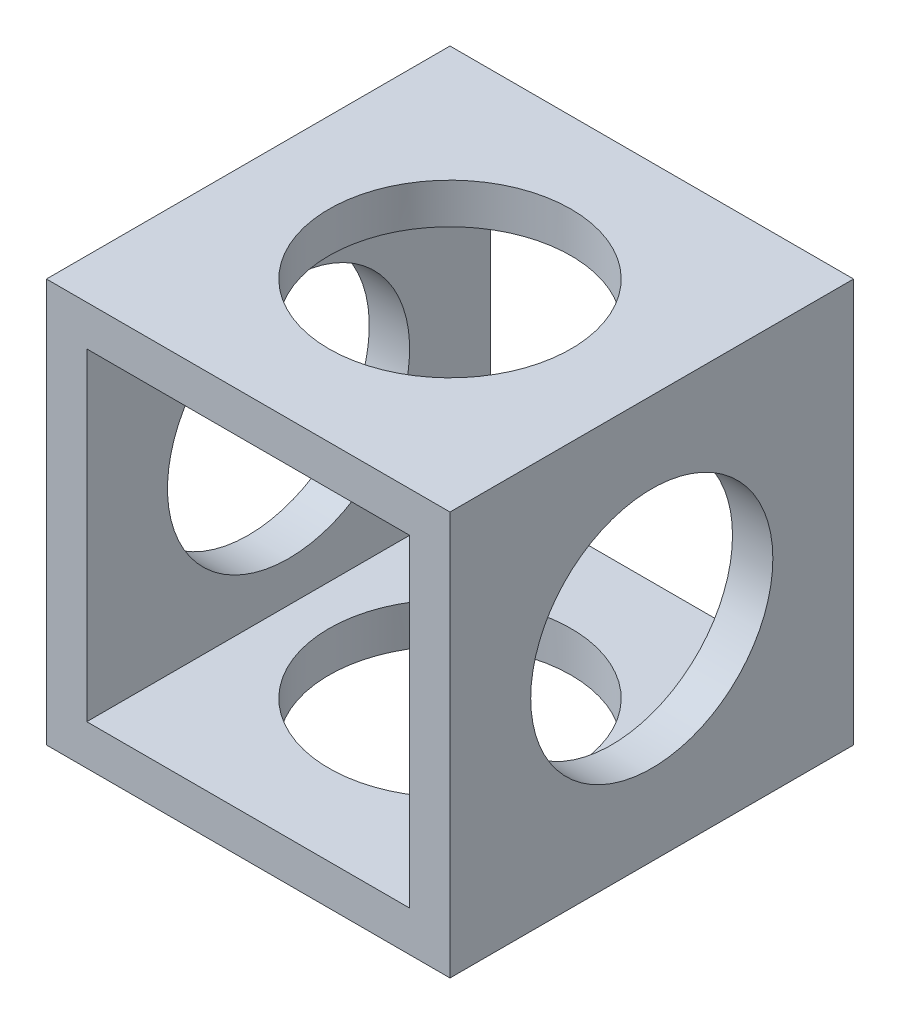
SolidWorks part; units mm, degrees
ref_plane "Alzado" through (0, 0, 0) normal (0, 0, 1) x (1, 0, 0)
ref_plane "Planta" through (0, 0, 0) normal (0, 1, 0) x (1, 0, 0)
ref_plane "Vista lateral" through (0, 0, 0) normal (1, 0, 0) x (0, 0, -1)
sketch "Croquis1" plane through (0, 0, 0) normal (0, 0, 1) x (1, 0, 0)
  line L1 (-25, -25) -> (25, -25)
  line L2 (-25, -25) -> (-25, 25)
  line L3 (-25, 25) -> (25, 25)
  line L4 (25, -25) -> (25, 25)
  line L5 (-25, -25) -> (25, 25) construction
  line L6 (-25, 25) -> (25, -25) construction
  line L7 (-20, -20) -> (20, -20)
  line L8 (-20, -20) -> (-20, 20)
  line L9 (-20, 20) -> (20, 20)
  line L10 (20, -20) -> (20, 20)
  line L11 (-20, -20) -> (20, 20) construction
  line L12 (-20, 20) -> (20, -20) construction
  point P0 (0, 0)
  point P6 (0, 0)
  point P11 (25, 28.1863)
  point P12 (25, 0)
  dimension "D1" = 50
  dimension "D2" = 50
  dimension "D3" = 5
extrude "Saliente-Extruir1" add sketch "Croquis1" against normal blind 50
sketch "Croquis2" plane through (0, 25, 0) normal (0, 1, 0) x (1, 0, 0)
  line L0 (25, 50) -> (25, 0) construction
  line L1 (25, 50) -> (25, 0)
  circle A0 centre (0, 25) radius 15
  point P4 (0, 0)
  point P5 (25, 25)
  point P6 (-4.8349, 25)
  dimension "D1" = 30
extrude "Cortar-Extruir1" cut sketch "Croquis2" against normal up to surface (50 mm away) contours A0 up to face at (0, -25, -25)
sketch "Croquis3" plane through (25, 0, 0) normal (1, 0, 0) x (0, 0, -1)
  line L0 (50, -25) -> (0, -25) construction
  circle A0 centre (25, 0) radius 15
  point P2 (0, 0)
  point P6 (25, -25)
  dimension "D1" = 30
extrude "Cortar-Extruir2" cut sketch "Croquis3" against normal up to surface (50 mm away) up to face at (-25, 0, -25)
